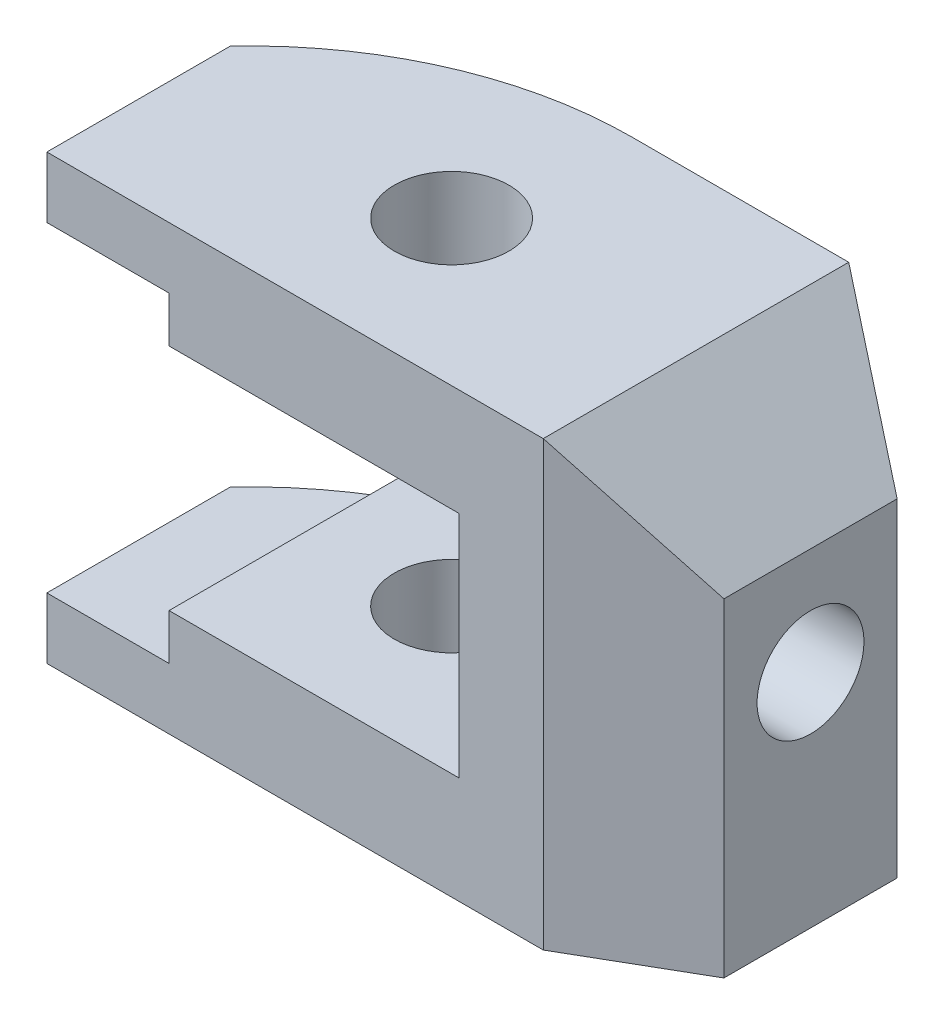
SolidWorks part; units mm, degrees
material "1060 Alloy"
ref_plane "Front Plane" through (0, 0, 0) normal (0, 0, 1) x (1, 0, 0)
ref_plane "Top Plane" through (0, 0, 0) normal (0, 1, 0) x (1, 0, 0)
ref_plane "Right Plane" through (0, 0, 0) normal (1, 0, 0) x (0, 0, -1)
sketch "Sketch1" plane through (0, 0, 0) normal (0, 1, 0) x (1, 0, 0)
  line L1 (0, 0) -> (65, 0)
  line L2 (0, 0) -> (0, 24)
  line L5 (0, 0) -> (65, 0)
  line L6 (0, 0) -> (0, 24)
  line L7 (36.6606, 40) -> (65, 40)
  line L8 (80, 8.6603) -> (80, 31.3397)
  line L9 (65, 0) -> (80, 8.6603)
  line L10 (65, 40) -> (80, 31.3397)
  circle A0 centre (34, 19) radius 7.5
  arc A1 (36.6606, 40) -> (0, 24) centre (36.6606, -10) ccw
  dimension "D6" = 15
  dimension "D11" = 50
  dimension "D1" = 24
  dimension "D2" = 65
  dimension "D3" = 19
  dimension "D4" = 80
  dimension "D5" = 40
  dimension "D7" = 31
  dimension "D8" = 30
  dimension "D9" = 30
  dimension "D10" = 15
extrude "Boss-Extrude1" add sketch "Sketch1" along normal blind 58 contours L7 A1 L2 L1 L9 L8 L10 A0
sketch "Sketch2" plane through (0, 0, -40) normal (0, 0, -1) x (-1, 0, 0)
  line L0 (0, 58) -> (0, 0) construction
  line L1 (0, 50) -> (-16, 50)
  line L2 (0, 50) -> (0, 8)
  line L3 (0, 8) -> (-16, 8)
  line L4 (-16, 50) -> (-16, 44)
  line L5 (0, 58) -> (-36.6606, 58) construction
  line L6 (-16, 44) -> (-54, 44)
  line L8 (-16, 14) -> (-54, 14)
  line L10 (-36.6606, 0) -> (0, 0) construction
  line L11 (-16, 14) -> (-16, 8)
  line L17 (-54, 44) -> (-54, 14)
  line L18 (-65, 58) -> (-65, 0) construction
  dimension "D1" = 8
  dimension "D2" = 8
  dimension "D3" = 6
  dimension "D4" = 6
  dimension "D5" = 16
  dimension "D6" = 11
extrude "Cut-Extrude1" cut sketch "Sketch2" against normal blind 58
sketch "Sketch3" plane through (0, 0, -40) normal (0, 0, -1) x (-1, 0, 0)
  line L0 (-80, 58) -> (-80, 43)
  line L1 (-80, 58) -> (-80, 0) construction
  line L2 (-80, 43) -> (-65, 58)
  line L3 (-65, 58) -> (-65, 0) construction
  line L4 (-65, 58) -> (-80, 58) construction
  line L5 (-65, 58) -> (-80, 58)
  line L6 (-80, 29) -> (-65, 29)
  line L7 (-80, 15) -> (-65, 0)
  line L8 (-80, 0) -> (-80, 15)
  line L9 (-65, 0) -> (-80, 0)
  dimension "D1" = 45
extrude "Cut-Extrude2" cut sketch "Sketch3" against normal blind 58
sketch "Sketch4" plane through (80, 0, 0) normal (1, 0, 0) x (0, 0, -1)
  line L0 (40, 58) -> (0, 58) construction
  line L2 (0, 58) -> (0, 0) construction
  circle A0 centre (20, 29) radius 7
  point P6 (20.2855, 33.9531)
  dimension "D1" = 14
  dimension "D2" = 29
  dimension "D3" = 20
extrude "Cut-Extrude3" cut sketch "Sketch4" against normal up to next
equation "\"A\"= 58.00"
equation "\"B\"= 40.00"
equation "\"C\"= 65.00"
